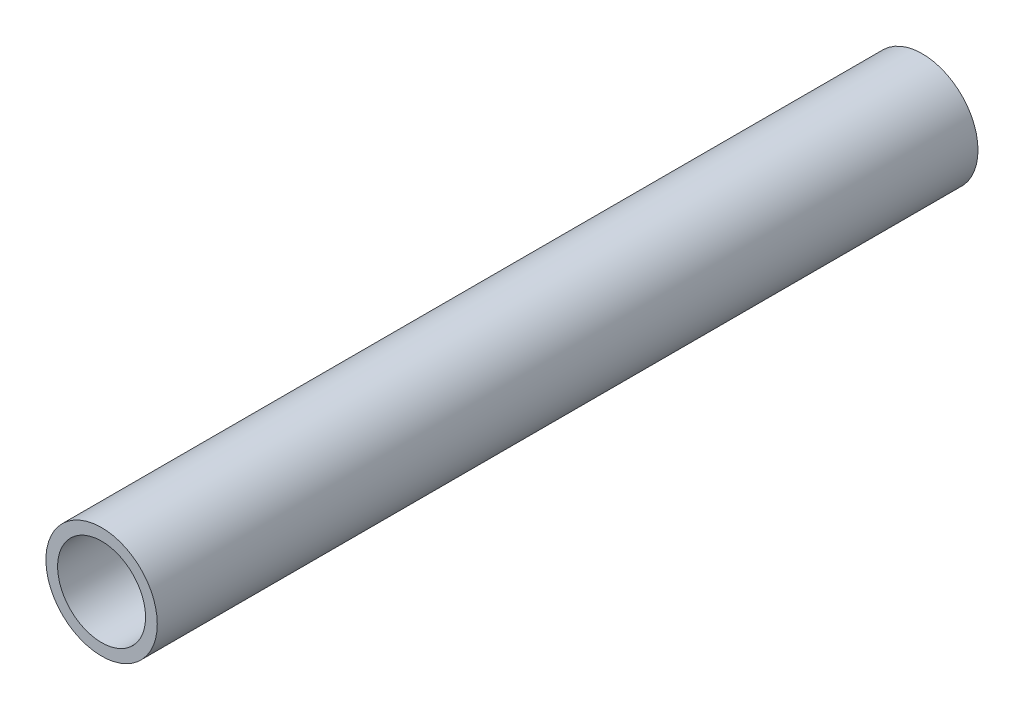
SolidWorks part; units mm, degrees
ref_plane "Front Plane" through (0, 0, 0) normal (0, 0, 1) x (1, 0, 0)
ref_plane "Top Plane" through (0, 0, 0) normal (0, 1, 0) x (1, 0, 0)
ref_plane "Right Plane" through (0, 0, 0) normal (1, 0, 0) x (0, 0, -1)
sketch "Sketch1" plane through (0, 0, 0) normal (0, 0, 1) x (1, 0, 0)
  circle A0 centre (0, 0) radius 4.75
  circle A1 centre (0, 0) radius 3.75
extrude "Boss-Extrude2" add sketch "Sketch1" along normal blind 70
